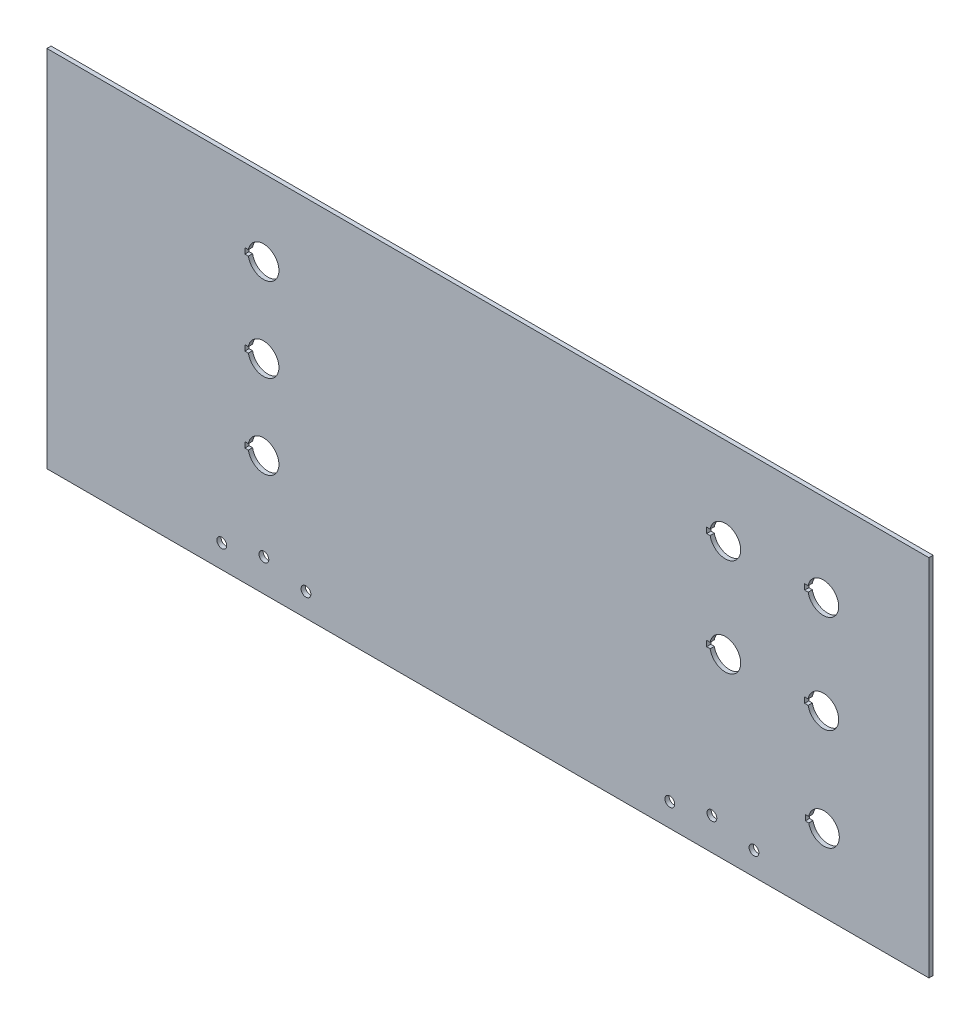
SolidWorks part; units mm, degrees
ref_plane "Alzado" through (0, 0, 0) normal (0, 0, 1) x (1, 0, 0)
ref_plane "Planta" through (0, 0, 0) normal (0, 1, 0) x (1, 0, 0)
ref_plane "Vista lateral" through (0, 0, 0) normal (1, 0, 0) x (0, 0, -1)
sketch "Croquis1" plane through (0, 0, 0) normal (0, 0, 1) x (1, 0, 0)
  line L1 (-315, 130) -> (315, 130)
  line L2 (-315, 130) -> (-315, -130)
  line L3 (-315, -130) -> (315, -130)
  line L4 (315, 130) -> (315, -130)
  line L5 (-315, 130) -> (315, -130) construction
  line L6 (-315, -130) -> (315, 130) construction
  point P0 (0, 0)
  dimension "D1" = 630
  dimension "D2" = 260
extrude "Saliente-Extruir1" add sketch "Croquis1" along normal blind 3
sketch "Croquis2" plane through (0, 0, 0) normal (0, 0, -1) x (-1, 0, 0)
  line L0 (315, -130) -> (-315, -130) construction
  line L1 (-315, -130) -> (-315, 130) construction
  line L2 (-228.7407, -0.4733) -> (-226.2407, -0.4733)
  line L3 (-229.1833, -73) -> (-226.6833, -73)
  line L5 (-229.1833, -77) -> (-226.6833, -77)
  line L6 (-226.6833, -73) -> (-226.6833, -77)
  line L7 (-228.7407, -4.4733) -> (-226.2407, -4.4733)
  line L8 (-226.2407, -0.4733) -> (-226.2407, -4.4733)
  line L15 (-158.7407, -0.4733) -> (-156.2407, -0.4733)
  line L16 (-156.2407, -0.4733) -> (-156.2407, -4.4733)
  line L17 (-158.7407, -4.4733) -> (-156.2407, -4.4733)
  line L18 (-158.7407, 69.5267) -> (-156.2407, 69.5267)
  line L19 (-156.2407, 69.5267) -> (-156.2407, 65.5267)
  line L20 (-158.7407, 65.5267) -> (-156.2407, 65.5267)
  line L21 (-228.7407, 69.5267) -> (-226.2407, 69.5267)
  line L22 (-226.2407, 69.5267) -> (-226.2407, 65.5267)
  line L23 (-228.7407, 65.5267) -> (-226.2407, 65.5267)
  line L24 (171.0914, -42.5178) -> (173.5914, -42.5178)
  line L25 (171.0914, -46.5178) -> (173.5914, -46.5178)
  line L26 (173.5914, -42.5178) -> (173.5914, -46.5178)
  line L27 (171.0914, 17.4822) -> (173.5914, 17.4822)
  line L28 (171.0914, 13.4822) -> (173.5914, 13.4822)
  line L29 (173.5914, 17.4822) -> (173.5914, 13.4822)
  line L30 (171.0914, 77.4822) -> (173.5914, 77.4822)
  line L31 (171.0914, 73.4822) -> (173.5914, 73.4822)
  line L32 (173.5914, 77.4822) -> (173.5914, 73.4822)
  arc A0 (-228.7407, -0.4733) -> (-228.7407, -4.4733) centre (-239.5574, -2.4733) ccw
  arc A2 (-163.5, -107) -> (-156.5, -107) centre (-160, -107) ccw
  arc A3 (-156.5, -107) -> (-163.5, -107) centre (-160, -107) ccw
  arc A4 (-163.5, -107) -> (-156.5, -107) centre (-160, -107) ccw
  arc A5 (-156.5, -107) -> (-163.5, -107) centre (-160, -107) ccw
  arc A6 (-133.45, -113.4) -> (-126.45, -113.4) centre (-129.95, -113.4) ccw
  arc A7 (-126.45, -113.4) -> (-133.45, -113.4) centre (-129.95, -113.4) ccw
  arc A8 (-133.45, -113.4) -> (-126.45, -113.4) centre (-129.95, -113.4) ccw
  arc A9 (-126.45, -113.4) -> (-133.45, -113.4) centre (-129.95, -113.4) ccw
  arc A10 (126.45, -113.4) -> (133.45, -113.4) centre (129.95, -113.4) ccw
  arc A11 (133.45, -113.4) -> (126.45, -113.4) centre (129.95, -113.4) ccw
  arc A12 (126.45, -113.4) -> (133.45, -113.4) centre (129.95, -113.4) ccw
  arc A13 (133.45, -113.4) -> (126.45, -113.4) centre (129.95, -113.4) ccw
  arc A14 (156.5, -107) -> (163.5, -107) centre (160, -107) ccw
  arc A15 (163.5, -107) -> (156.5, -107) centre (160, -107) ccw
  arc A16 (156.5, -107) -> (163.5, -107) centre (160, -107) ccw
  arc A17 (163.5, -107) -> (156.5, -107) centre (160, -107) ccw
  arc A18 (186.55, -113.4) -> (193.55, -113.4) centre (190.05, -113.4) ccw
  arc A19 (193.55, -113.4) -> (186.55, -113.4) centre (190.05, -113.4) ccw
  arc A20 (186.55, -113.4) -> (193.55, -113.4) centre (190.05, -113.4) ccw
  arc A21 (193.55, -113.4) -> (186.55, -113.4) centre (190.05, -113.4) ccw
  arc A22 (-193.55, -113.4) -> (-186.55, -113.4) centre (-190.05, -113.4) ccw
  arc A23 (-186.55, -113.4) -> (-193.55, -113.4) centre (-190.05, -113.4) ccw
  arc A24 (-193.55, -113.4) -> (-186.55, -113.4) centre (-190.05, -113.4) ccw
  arc A25 (-186.55, -113.4) -> (-193.55, -113.4) centre (-190.05, -113.4) ccw
  arc A63 (-158.7407, -0.4733) -> (-158.7407, -4.4733) centre (-169.5574, -2.4733) ccw
  arc A64 (-158.7407, 69.5267) -> (-158.7407, 65.5267) centre (-169.5574, 67.5267) ccw
  arc A65 (-228.7407, 69.5267) -> (-228.7407, 65.5267) centre (-239.5574, 67.5267) ccw
  arc A66 (171.0914, -42.5178) -> (171.0914, -46.5178) centre (160.2747, -44.5178) ccw
  arc A67 (171.0914, 17.4822) -> (171.0914, 13.4822) centre (160.2747, 15.4822) ccw
  arc A68 (171.0914, 77.4822) -> (171.0914, 73.4822) centre (160.2747, 75.4822) ccw
  arc A180 (-229.1833, -73) -> (-229.1833, -77) centre (-240, -75) ccw
  point P30 (-229, -75)
  dimension "D9" = 22
  dimension "D7" = 55
  dimension "D8" = 75
  dimension "D10" = 4
  dimension "D11" = 2.5
  dimension "D1" = 0
  dimension "D2" = 0
  dimension "D3" = 0
  dimension "D4" = 0
  dimension "D5" = 0
  dimension "D6" = 0
  dimension "D12" = 2
  dimension "D13" = 2
extrude "Cortar-Extruir1" cut sketch "Croquis2" against normal through all
